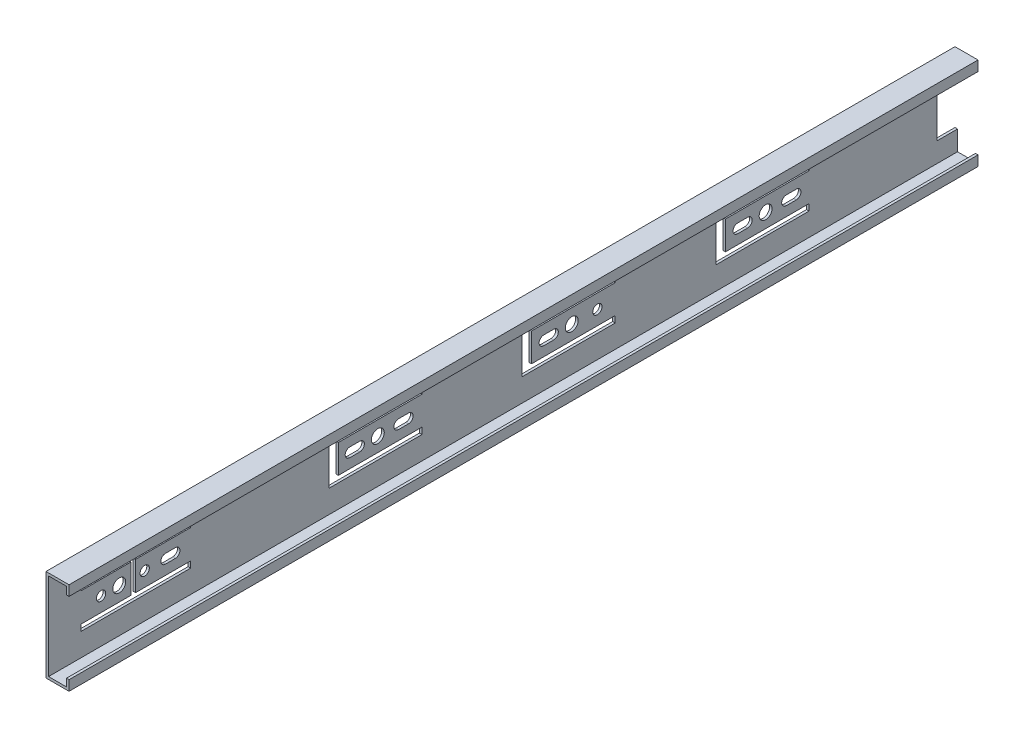
SolidWorks part; units mm, degrees
ref_plane "Front Plane" through (0, 0, 0) normal (0, 0, 1) x (1, 0, 0)
ref_plane "Top Plane" through (0, 0, 0) normal (0, 1, 0) x (1, 0, 0)
ref_plane "Right Plane" through (0, 0, 0) normal (1, 0, 0) x (0, 0, -1)
ref_plane "Plane1" through (5.7, 0, 0) normal (1, 0, 0) x (0, 0, -1)
sketch "Sketch1" plane through (5.7, 0, 0) normal (1, 0, 0) x (0, 0, -1)
  line L0 (0, -22.85) -> (0, 22.85)
  line L1 (0, 22.85) -> (-450, 22.85)
  line L2 (-450, 22.85) -> (-450, -22.85)
  line L3 (-450, -22.85) -> (0, -22.85)
extrude "Boss-Extrude1" add sketch "Sketch1" against normal blind 11.4
sketch "Sketch2" plane through (0, 0, 450) normal (0, 0, 1) x (1, 0, 0)
  line L0 (5.7, 17.85) -> (4.43, 17.85)
  line L1 (4.43, 17.85) -> (4.43, 21.58)
  line L2 (4.43, 21.58) -> (-4.43, 21.58)
  line L3 (-4.43, 21.58) -> (-4.43, -21.58)
  line L4 (-4.43, -21.58) -> (4.43, -21.58)
  line L5 (4.43, -21.58) -> (4.43, -17.85)
  line L6 (4.43, -17.85) -> (5.7, -17.85)
  line L7 (5.7, -17.85) -> (5.7, 17.85)
extrude "Cut-Extrude1" cut sketch "Sketch2" against normal through all
sketch "Sketch3" plane through (-5.7, 0, 0) normal (-1, 0, 0) x (0, 0, 1)
  line L0 (0, 11.8) -> (0, -11.8)
  line L1 (0, -11.8) -> (10.25, -11.8)
  line L2 (10.25, -11.8) -> (10.25, 11.8)
  line L3 (10.25, 11.8) -> (0, 11.8)
extrude "Cut-Extrude2" cut sketch "Sketch3" against normal through all
sketch "Sketch4" plane through (-4.43, 0, 0) normal (1, 0, 0) x (0, 0, -1)
  line L0 (-169.5, -10.25) -> (-169.5, -7.05)
  line L1 (-169.5, -7.05) -> (-210.9, -7.05)
  line L2 (-210.9, -7.05) -> (-210.9, 7.05)
  line L3 (-210.9, 7.05) -> (-169.5, 7.05)
  line L4 (-169.5, 7.05) -> (-169.5, 10.25)
  line L5 (-169.5, 10.25) -> (-215.5, 10.25)
  line L6 (-215.5, 10.25) -> (-215.5, -10.25)
  line L7 (-215.5, -10.25) -> (-169.5, -10.25)
extrude "Cut-Extrude3" cut sketch "Sketch4" against normal through all
sketch "Sketch5" plane through (-4.43, 0, 0) normal (1, 0, 0) x (0, 0, -1)
  line L0 (-119.5, -10.25) -> (-73.5, -10.25)
  line L1 (-73.5, -10.25) -> (-73.5, -7.05)
  line L2 (-73.5, -7.05) -> (-114.9, -7.05)
  line L3 (-114.9, -7.05) -> (-114.9, 7.05)
  line L4 (-114.9, 7.05) -> (-73.5, 7.05)
  line L5 (-73.5, 7.05) -> (-73.5, 10.25)
  line L6 (-73.5, 10.25) -> (-119.5, 10.25)
  line L7 (-119.5, 10.25) -> (-119.5, -10.25)
extrude "Cut-Extrude4" cut sketch "Sketch5" against normal through all
sketch "Sketch6" plane through (-4.43, 0, 0) normal (1, 0, 0) x (0, 0, -1)
  line L0 (-265.15, 7.05) -> (-265.15, 10.25)
  line L1 (-265.15, 10.25) -> (-311.15, 10.25)
  line L2 (-311.15, 10.25) -> (-311.15, -10.25)
  line L3 (-311.15, -10.25) -> (-265.15, -10.25)
  line L4 (-265.15, -10.25) -> (-265.15, -7.05)
  line L5 (-265.15, -7.05) -> (-306.55, -7.05)
  line L6 (-306.55, -7.05) -> (-306.55, 7.05)
  line L7 (-306.55, 7.05) -> (-265.15, 7.05)
extrude "Cut-Extrude5" cut sketch "Sketch6" against normal through all
sketch "Sketch7" plane through (-4.43, 0, 0) normal (1, 0, 0) x (0, 0, -1)
  line L0 (-79.85, 2.3) -> (-84.75, 2.3)
  line L1 (-84.75, -2.3) -> (-79.85, -2.3)
  arc A0 (-79.85, -2.3) -> (-79.85, 2.3) centre (-79.85, 0) ccw
  arc A1 (-84.75, 2.3) -> (-84.75, -2.3) centre (-84.75, 0) ccw
extrude "Cut-Extrude6" cut sketch "Sketch7" against normal through all
sketch "Sketch8" plane through (-4.43, 0, 0) normal (1, 0, 0) x (0, 0, -1)
  line L0 (-108.85, -2.3) -> (-103.95, -2.3)
  line L1 (-103.95, 2.3) -> (-108.85, 2.3)
  arc A0 (-103.95, -2.3) -> (-103.95, 2.3) centre (-103.95, 0) ccw
  arc A1 (-108.85, 2.3) -> (-108.85, -2.3) centre (-108.85, 0) ccw
extrude "Cut-Extrude7" cut sketch "Sketch8" against normal through all
sketch "Sketch9" plane through (-4.43, 0, 0) normal (1, 0, 0) x (0, 0, -1)
  line L0 (-387.25, 2.3) -> (-392.15, 2.3)
  line L1 (-392.15, -2.3) -> (-387.25, -2.3)
  arc A0 (-387.25, -2.3) -> (-387.25, 2.3) centre (-387.25, 0) ccw
  arc A1 (-392.15, 2.3) -> (-392.15, -2.3) centre (-392.15, 0) ccw
extrude "Cut-Extrude8" cut sketch "Sketch9" against normal through all
sketch "Sketch10" plane through (-4.43, 0, 0) normal (1, 0, 0) x (0, 0, -1)
  line L0 (-199.95, 2.3) -> (-204.85, 2.3)
  line L1 (-204.85, -2.3) -> (-199.95, -2.3)
  arc A0 (-204.85, 2.3) -> (-204.85, -2.3) centre (-204.85, 0) ccw
  arc A1 (-199.95, -2.3) -> (-199.95, 2.3) centre (-199.95, 0) ccw
extrude "Cut-Extrude9" cut sketch "Sketch10" against normal through all
sketch "Sketch11" plane through (-4.43, 0, 0) normal (1, 0, 0) x (0, 0, -1)
  line L0 (-295.95, 2.3) -> (-300.85, 2.3)
  line L1 (-300.85, -2.3) -> (-295.95, -2.3)
  arc A0 (-295.95, -2.3) -> (-295.95, 2.3) centre (-295.95, 0) ccw
  arc A1 (-300.85, 2.3) -> (-300.85, -2.3) centre (-300.85, 0) ccw
extrude "Cut-Extrude10" cut sketch "Sketch11" against normal through all
sketch "Sketch12" plane through (-4.43, 0, 0) normal (1, 0, 0) x (0, 0, -1)
  line L0 (-271.85, 2.3) -> (-276.75, 2.3)
  line L1 (-276.75, -2.3) -> (-271.85, -2.3)
  arc A0 (-276.75, 2.3) -> (-276.75, -2.3) centre (-276.75, 0) ccw
  arc A1 (-271.85, -2.3) -> (-271.85, 2.3) centre (-271.85, 0) ccw
extrude "Cut-Extrude11" cut sketch "Sketch12" against normal through all
sketch "Sketch13" plane through (-5.7, 0, 0) normal (-1, 0, 0) x (0, 0, 1)
  line L0 (434, -7.15) -> (409.2, -7.15)
  line L1 (409.2, -7.15) -> (409.2, 7.15)
  line L2 (409.2, 7.15) -> (434, 7.15)
  line L3 (434, 7.15) -> (434, 10.25)
  line L4 (434, 10.25) -> (379.65, 10.25)
  line L5 (379.65, 10.25) -> (379.65, 7.15)
  line L6 (379.65, 7.15) -> (406.9, 7.15)
  line L7 (406.9, 7.15) -> (406.9, -7.15)
  line L8 (406.9, -7.15) -> (379.65, -7.15)
  line L9 (379.65, -7.15) -> (379.65, -10.25)
  line L10 (379.65, -10.25) -> (434, -10.25)
  line L11 (434, -10.25) -> (434, -7.15)
extrude "Cut-Extrude12" cut sketch "Sketch13" against normal through all
hole_wizard "Ø6.4 (6.4) Diameter Hole1" positions "Sketch15" profile "Sketch14" hole size "Ø6.4" standard "ANSI Metric"
sketch "Sketch15" plane through (-5.7, 0, 0) normal (-1, 0, 0) x (0, 0, 1)
  point P0 (415, 0)
  point P1 (287, 0)
  point P2 (191, 0)
  point P3 (95, 0)
sketch "Sketch14" plane through (-5.7, 0, 415) normal (0, 1, 0) x (0, 0, 1)
  line L0 (0, 0) -> (0, 11.4)
  line L1 (0, 11.4) -> (3.2, 11.4)
  line L2 (3.2, 11.4) -> (3.2, 0)
  line L5 (3.2, 0) -> (0, 0)
  line L11 (0, -6.35) -> (0, 107.95) construction
  dimension "Thru Hole Dia." = 6.4
  dimension "Thru Hole Depth" = 11.4
hole_wizard "Ø4.6 (4.6) Diameter Hole1" positions "Sketch17" profile "Sketch16" hole size "Ø4.6" standard "ANSI Metric"
sketch "Sketch17" plane through (-5.7, 0, 0) normal (-1, 0, 0) x (0, 0, 1)
  point P0 (424, 0)
  point P1 (402.4, 0)
  point P2 (178.3, 0)
sketch "Sketch16" plane through (-5.7, 0, 424) normal (0, 1, 0) x (0, 0, 1)
  line L0 (0, 0) -> (0, 11.4)
  line L1 (0, 11.4) -> (2.3, 11.4)
  line L2 (2.3, 11.4) -> (2.3, 0)
  line L5 (2.3, 0) -> (0, 0)
  line L11 (0, -6.35) -> (0, 107.95) construction
  dimension "Thru Hole Dia." = 4.6
  dimension "Thru Hole Depth" = 11.4
scale "Scale1" scale about centroid uniform scaling yes scale factor 0.25
